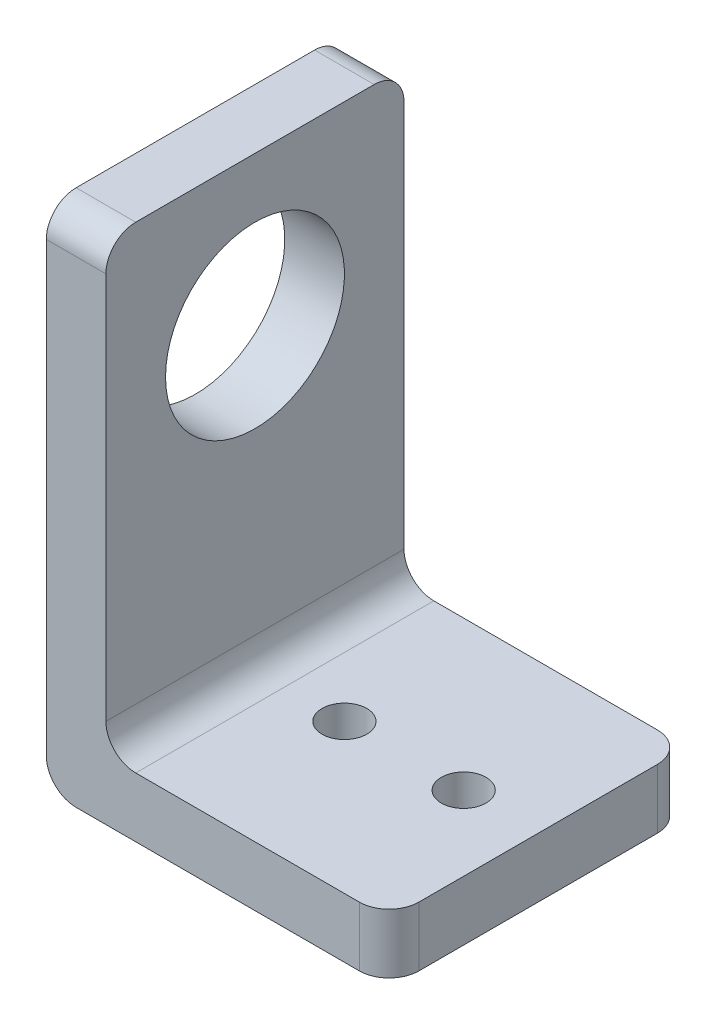
SolidWorks part; units mm, degrees
material "Acrylic (Medium-high impact)"
ref_plane "Front Plane" through (0, 0, 0) normal (0, 0, 1) x (1, 0, 0)
ref_plane "Top Plane" through (0, 0, 0) normal (0, 1, 0) x (1, 0, 0)
ref_plane "Right Plane" through (0, 0, 0) normal (1, 0, 0) x (0, 0, -1)
sketch "Sketch1" plane through (0, 0, 0) normal (0, 0, 1) x (1, 0, 0)
  line L0 (0, 0) -> (23, 0)
  line L1 (23, 0) -> (23, 4)
  line L2 (23, 4) -> (4, 4)
  line L3 (4, 4) -> (4, 34)
  line L4 (4, 34) -> (0, 34)
  line L5 (0, 34) -> (0, 0)
extrude "Boss-Extrude1" add sketch "Sketch1" along normal blind 20
sketch "Sketch2" plane through (0, 0, 0) normal (-1, 0, 0) x (0, 0, 1)
  line L0 (20, 34) -> (0, 34) construction
  line L2 (0, 34) -> (0, 0) construction
  circle A0 centre (10, 24) radius 6
  dimension "D1" = 10
  dimension "D2" = 10
extrude "Cut-Extrude1" cut sketch "Sketch2" against normal blind 4
sketch "Sketch3" plane through (0, 4, 0) normal (0, 1, 0) x (1, 0, 0)
  line L1 (23, 0) -> (4, 0) construction
  line L3 (0, -20) -> (0, 0) construction
  circle A0 centre (18, -10) radius 1.5
  circle A1 centre (10, -10) radius 1.5
  dimension "D1" = 10
  dimension "D2" = 8
  dimension "D3" = 10
extrude "Cut-Extrude2" cut sketch "Sketch3" against normal blind 4
fillet "Fillet1" radius 2 6 edges at (23, 2, 0) (23, 2, 20) (4, 4, 10) (0, 0, 10) (2, 34, 0) (2, 34, 20)
